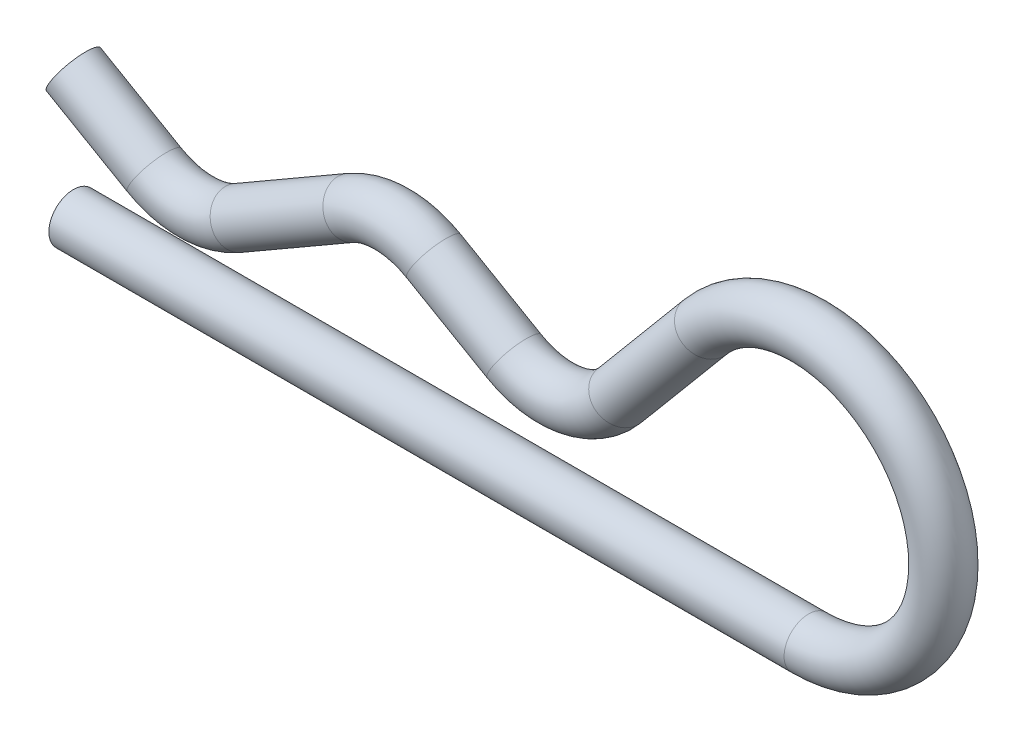
SolidWorks part; units mm, degrees
material "Corde à piano"
ref_plane "Face" through (0, 0, 0) normal (0, 0, 1) x (1, 0, 0)
ref_plane "Dessus" through (0, 0, 0) normal (0, 1, 0) x (1, 0, 0)
ref_plane "Droite" through (0, 0, 0) normal (1, 0, 0) x (0, 0, -1)
sketch "Esquisse1" plane through (0, 0, 0) normal (0, 0, 1) x (1, 0, 0)
  line L0 (0, 0) -> (15, 0)
  line L1 (12.8934, 4.5177) -> (11.1433, 2.432)
  line L2 (8.9911, 2.0525) -> (7.35, 3)
  line L3 (5.65, 3) -> (3.35, 1.6721)
  line L4 (1.65, 1.6721) -> (0, 2.6247)
  arc A0 (15, 0) -> (12.8934, 4.5177) centre (15, 2.75) ccw
  arc A1 (11.1433, 2.432) -> (8.9911, 2.0525) centre (9.8411, 3.5248) cw
  arc A2 (7.35, 3) -> (5.65, 3) centre (6.5, 1.5278) ccw
  arc A3 (3.35, 1.6721) -> (1.65, 1.6721) centre (2.5, 3.1443) cw
  dimension "D2" = 1.7
  dimension "D3" = 2.75
  dimension "D1" = 15
  dimension "D4" = 50
  dimension "D5" = 120
  dimension "D6" = 3
  dimension "D7" = 30
  dimension "D8" = 6.5
  dimension "D9" = 2.5
sketch "Esquisse2" plane through (0, 0, 0) normal (1, 0, 0) x (0, 0, -1)
  circle A0 centre (0, 0) radius 0.5
  dimension "D1" = 1
sweep "Balayage1" add profiles "Esquisse2" path "Esquisse1"
